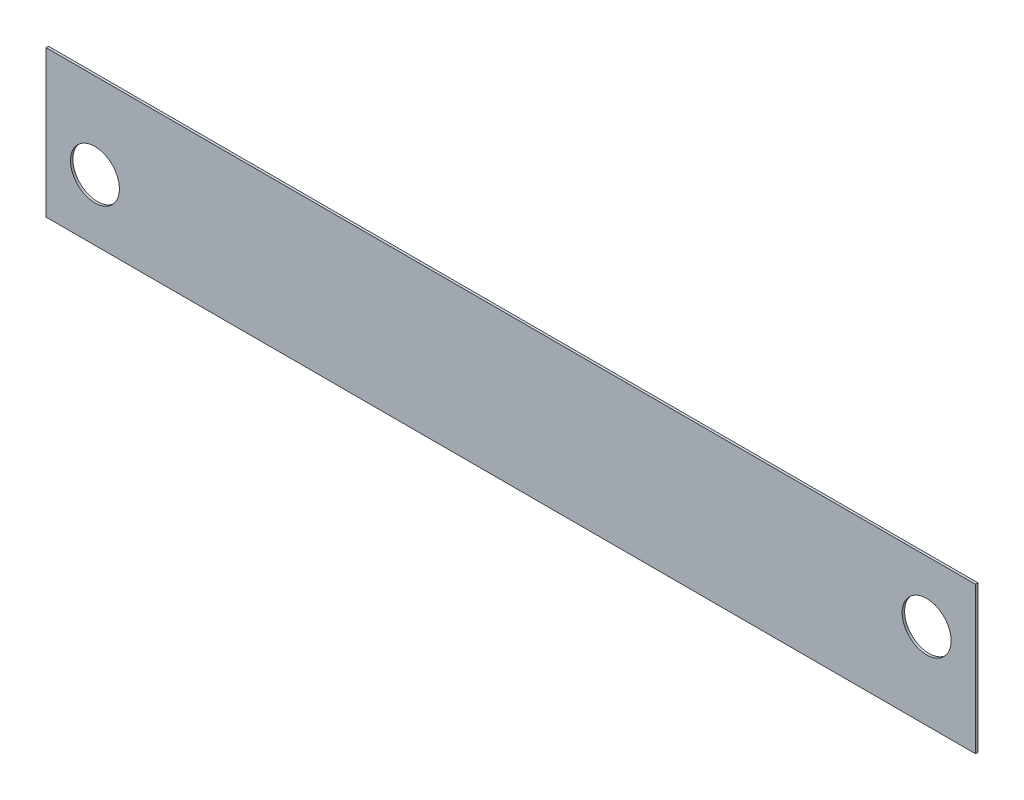
SolidWorks part; units mm, degrees
ref_plane "Plane1" through (0, 0, 0) normal (0, 0, 1) x (1, 0, 0)
ref_plane "Plane2" through (0, 0, 0) normal (0, 1, 0) x (1, 0, 0)
ref_plane "Plane3" through (0, 0, 0) normal (1, 0, 0) x (0, 0, -1)
sketch "Sketch1" plane through (0, 0, 0) normal (0, 0, 1) x (1, 0, 0)
  line L0 (0, 0) -> (340, 0) construction
  line L1 (340, 0) -> (340, 10) construction
  line L2 (-20, -25) -> (360, -25)
  line L3 (360, 35) -> (-20, 35)
  line L4 (360, 35) -> (360, -25)
  line L5 (-20, -25) -> (-20, 35)
  circle A0 centre (0, 0) radius 10
  circle A1 centre (340, 10) radius 10
  dimension "D1" = 20
  dimension "D4" = 25
  dimension "D2" = 340
  dimension "D3" = 10
  dimension "D5" = 20
  dimension "D6" = 25
  dimension "D7" = 20
extrude "Extrude1" add sketch "Sketch1" along normal blind 1
